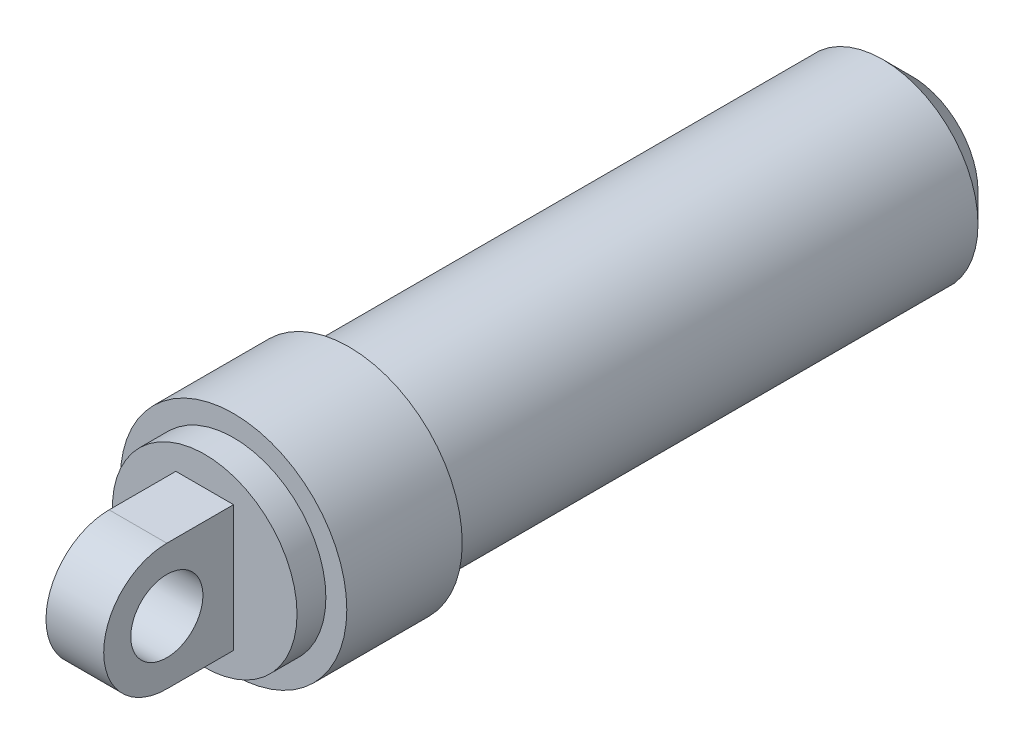
SolidWorks part; units mm, degrees
ref_plane "Front Plane" through (0, 0, 0) normal (0, 0, 1) x (1, 0, 0)
ref_plane "Top Plane" through (0, 0, 0) normal (0, 1, 0) x (1, 0, 0)
ref_plane "Right Plane" through (0, 0, 0) normal (1, 0, 0) x (0, 0, -1)
sketch "Sketch2" plane through (0, 0, 0) normal (0, 0, 1) x (1, 0, 0)
  circle A0 centre (0, 0) radius 6.6
  dimension "D1" = 13.2
extrude "External Shock" add sketch "Sketch2" along normal blind 39
chamfer "Shock Chamfer" distance 2 angle 45 1 edges at (6.6, 0, 0)
sketch "Sketch3" plane through (0, 0, 39) normal (0, 0, 1) x (1, 0, 0)
  circle A0 centre (0, 0) radius 7.85
  dimension "D1" = 15.7
extrude "Cylinder A" add sketch "Sketch3" along normal blind 8
sketch "Sketch4" plane through (0, 0, 47) normal (0, 0, 1) x (1, 0, 0)
  circle A0 centre (0, 0) radius 6.4
  dimension "D1" = 12.8
extrude "Cylinder B" add sketch "Sketch4" along normal blind 2
sketch "Sketch5" plane through (0, 0, 0) normal (1, 0, 0) x (0, 0, -1)
  line L0 (-53.625, -4.375) -> (-49, -4.375)
  line L1 (-49, 6.4) -> (-49, -6.4) construction
  line L2 (-49, -4.375) -> (-49, 4.375)
  line L3 (-49, 4.375) -> (-53.625, 4.375)
  arc A0 (-53.625, -4.375) -> (-53.625, 4.375) centre (-53.625, 0) cw
  point P10 (-58, 0)
  dimension "D1" = 4.375
  dimension "D2" = 9
extrude "Mounting Boss" add sketch "Sketch5" along normal mid plane 4
sketch "Sketch6" plane through (-2, 0, 0) normal (-1, 0, 0) x (0, 0, 1)
  circle A0 centre (53.625, 0) radius 2.5
  arc A1 (53.625, -4.375) -> (53.625, 4.375) centre (53.625, 0) ccw construction
  dimension "D1" = 5
extrude "Mounting Hole" cut sketch "Sketch6" against normal blind 4
sketch "Sketch7" plane through (0, 0, 0) normal (0, 0, -1) x (-1, 0, 0)
  circle A0 centre (0, 0) radius 1.5
  dimension "D1" = 3
extrude "Inner Hole" cut sketch "Sketch7" against normal blind 35
